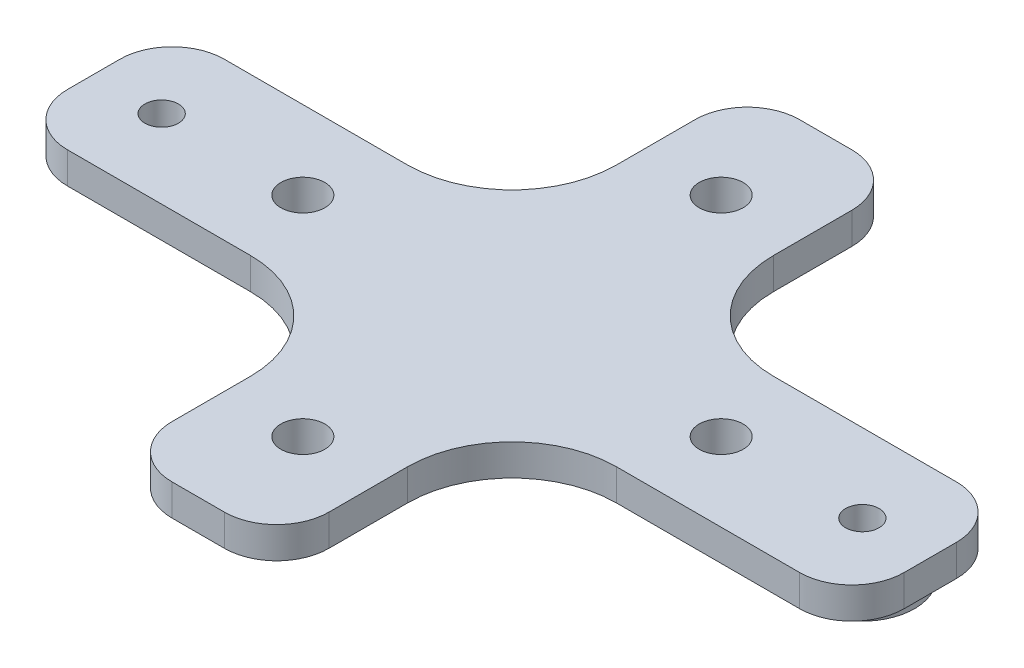
SolidWorks part; units mm, degrees
ref_plane "Front Plane" through (0, 0, 0) normal (0, 0, 1) x (1, 0, 0)
ref_plane "Top Plane" through (0, 0, 0) normal (0, 1, 0) x (1, 0, 0)
ref_plane "Right Plane" through (0, 0, 0) normal (1, 0, 0) x (0, 0, -1)
sketch "草圖2" plane through (0, 0, 0) normal (0, 1, 0) x (1, 0, 0)
  line L1 (-40, 7.5) -> (40, 7.5)
  line L2 (-40, 7.5) -> (-40, -7.5)
  line L3 (-40, -7.5) -> (40, -7.5)
  line L4 (40, 7.5) -> (40, -7.5)
  line L5 (-40, 7.5) -> (40, -7.5) construction
  line L6 (-40, -7.5) -> (40, 7.5) construction
  point P0 (0, 0)
  dimension "D1" = 80
  dimension "D2" = 15
extrude "填料-伸長1" add sketch "草圖2" along normal blind 3
sketch "草圖1" plane through (0, 0, 0) normal (0, 1, 0) x (1, 0, 0)
  line L0 (-33.5, 0) -> (33.5, 0) construction
  circle A0 centre (-33.5, 0) radius 5
  circle A1 centre (33.5, 0) radius 5
  point P4 (0, 0)
  dimension "D2" = 10
  dimension "D1" = 67
extrude "填料-伸長2" add sketch "草圖1" against normal blind 2
sketch "草圖3" plane through (0, 0, 0) normal (0, -1, 0) x (1, 0, 0)
  line L1 (-7.5, 30) -> (7.5, 30)
  line L2 (-7.5, 30) -> (-7.5, -30)
  line L3 (-7.5, -30) -> (7.5, -30)
  line L4 (7.5, 30) -> (7.5, -30)
  line L5 (-7.5, 30) -> (7.5, -30) construction
  line L6 (-7.5, -30) -> (7.5, 30) construction
  point P0 (0, 0)
  dimension "D1" = 60
  dimension "D2" = 15
extrude "填料-伸長3" add sketch "草圖3" against normal blind 3
sketch "草圖4" plane through (0, 0, 0) normal (0, -1, 0) x (1, 0, 0)
  line L0 (0, 0) -> (0, 20) construction
  line L1 (0, 0) -> (0, -20) construction
  circle A0 centre (0, 20) radius 2.1
  circle A1 centre (0, -20) radius 2.1
  dimension "D2" = 4.2
  dimension "D1" = 20
extrude "除料-伸長4" cut sketch "草圖4" against normal through all
sketch "草圖5" plane through (0, 0, 0) normal (0, -1, 0) x (1, 0, 0)
  line L0 (-20, 0) -> (0, 0) construction
  line L1 (0, 0) -> (20, 0) construction
  circle A0 centre (-20, 0) radius 2.1
  circle A1 centre (20, 0) radius 2.1
  dimension "D2" = 4.2
  dimension "D1" = 20
extrude "除料-伸長5" cut sketch "草圖5" against normal through all
fillet "圓角2" radius 5 8 edges at (-7.5, 1.5, 30) (7.5, 1.5, 30) (40, 1.5, 7.5) (40, 1.5, -7.5) (7.5, 1.5, -30) (-7.5, 1.5, -30) (-40, 1.5, -7.5) (-40, 1.5, 7.5)
sketch "草圖6" plane through (0, -2, 0) normal (0, -1, 0) x (1, 0, 0)
  circle A0 centre (-33.5, 0) radius 1.6
  circle A1 centre (33.5, 0) radius 1.6
  dimension "D1" = 3.2
extrude "除料-伸長6" cut sketch "草圖6" against normal through all
fillet "圓角3" radius 10 4 edges at (7.5, 1.5, 7.5) (7.5, 1.5, -7.5) (-7.5, 1.5, 7.5) (-7.5, 1.5, -7.5)
